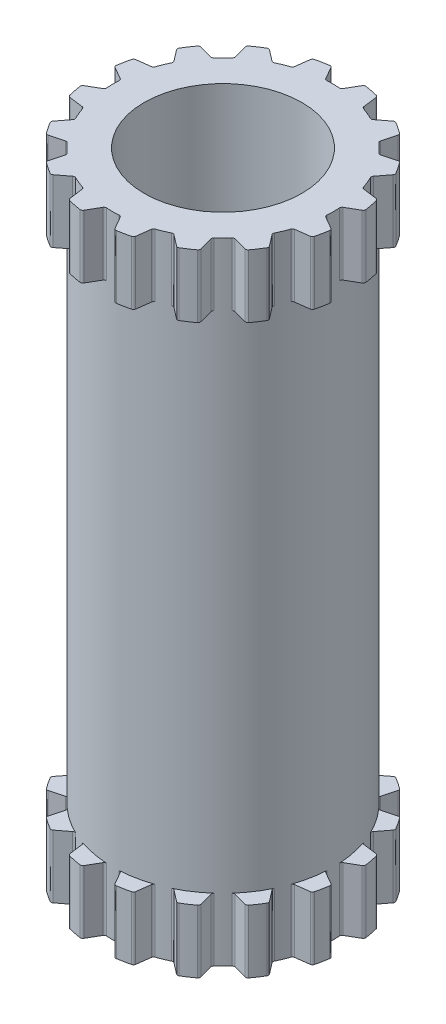
SolidWorks part; units mm, degrees
material "Brass"
ref_plane "Front Plane" through (0, 0, 0) normal (0, 0, 1) x (1, 0, 0)
ref_plane "Top Plane" through (0, 0, 0) normal (0, 1, 0) x (1, 0, 0)
ref_plane "Right Plane" through (0, 0, 0) normal (1, 0, 0) x (0, 0, -1)
ref_axis "CentralAxis" through (0, 5.5, 0) along (0, -1, 0)
sketch "BodyS" plane through (0, 0, 0) normal (0, 0, 1) x (1, 0, 0)
  line L0 (0, 5) -> (2, 5)
  line L1 (2, 5) -> (2, -5)
  line L6 (2, -5) -> (0, -5)
  line L7 (0, -5) -> (0, 5) construction
  dimension "Height" = 10
  dimension "ThreadInsertDiameter" = 4
revolve "Body" add sketch "BodyS" angle 360 about L7
hole_wizard "M3x0.5 Tapped Hole1" positions "Sketch2" profile "Sketch3" tap size "M3x0.5" standard "ANSI Metric" end condition through all
sketch "Sketch2" plane through (0, 5, 0) normal (0, 1, 0) x (1, 0, 0)
  point P0 (0, 0)
sketch "Sketch3" plane through (0, 5, 0) normal (1, 0, 0) x (0, 0, 1)
  line L0 (0, 0) -> (0, 10)
  line L1 (0, 10) -> (1.25, 10)
  line L2 (1.25, 10) -> (1.25, 0)
  line L5 (1.25, 0) -> (0, 0)
  line L11 (0, -6.35) -> (0, 107.95) construction
  dimension "Thru Tap Drill Dia." = 2.5
  dimension "Thru Tap Drill Depth" = 10
cosmetic thread "Hole Thread1" parameters "D2"=3
sketch "MidBodyCutS" plane through (0, 0, 0) normal (0, 0, 1) x (1, 0, 0)
  line L1 (2, 4) -> (1.75, 4)
  line L2 (2, 4) -> (2, -4)
  line L3 (2, -4) -> (1.75, -4)
  line L4 (1.75, 4) -> (1.75, -4)
  line L5 (2, 4) -> (1.75, -4) construction
  line L6 (2, -4) -> (1.75, 4) construction
  line L7 (2, -5) -> (2, 5) construction
  line L8 (0, 0) -> (1.875, 0) construction
  line L9 (2, 5) -> (-2, 5) construction
  point P0 (1.875, 0)
  dimension "Width" = 0.25
  dimension "RefHeight" = 8
  dimension "Height" = 1
revolve "MidBodyCut" cut sketch "MidBodyCutS" angle 360 about axis through (0, 5.5, 0) along (0, -1, 0)
sketch "GrooveCutS" plane through (0, 0, 0) normal (0, 1, 0) x (1, 0, 0)
  line L4 (0, 0) -> (0, 1.75) construction
  line L5 (0.1369, 1.7671) -> (0.248, 1.9595)
  line L6 (0, 1.75) -> (0, 2) construction
  line L7 (-0.1369, 1.7671) -> (-0.248, 1.9595)
  circle A0 centre (0, 0) radius 1.75 construction
  circle A1 centre (0, 0) radius 2 construction
  arc A2 (0.0999, 1.7471) -> (-0.0999, 1.7471) centre (0, 0) ccw
  arc A3 (0.2884, 1.9791) -> (-0.2884, 1.9791) centre (0, 0) ccw
  arc A4 (0.248, 1.9595) -> (0.2884, 1.9791) centre (0.2826, 1.9395) cw
  arc A5 (0.1369, 1.7671) -> (0.0999, 1.7471) centre (0.1022, 1.7871) cw
  arc A6 (-0.248, 1.9595) -> (-0.2884, 1.9791) centre (-0.2826, 1.9395) ccw
  arc A7 (-0.1369, 1.7671) -> (-0.0999, 1.7471) centre (-0.1022, 1.7871) ccw
  point P14 (0.1245, 1.7456)
  dimension "RefInnerDiameter" = 3.5
  dimension "InnerRadius" = 0.04
  dimension "OuterRadius" = 0.04
  dimension "Depth" = 0.25
  dimension "Angle" = 60
  dimension "RefOuterWidth" = 0.5768
  dimension "InnerArcWidth" = 0.2
extrude "GrooveCut" cut sketch "GrooveCutS" against normal through all both and the other way through all
pattern_circular "GCCP" count 16 over 360 about axis through (0, 0, 0) along (0, 1, 0) of "GrooveCut"
